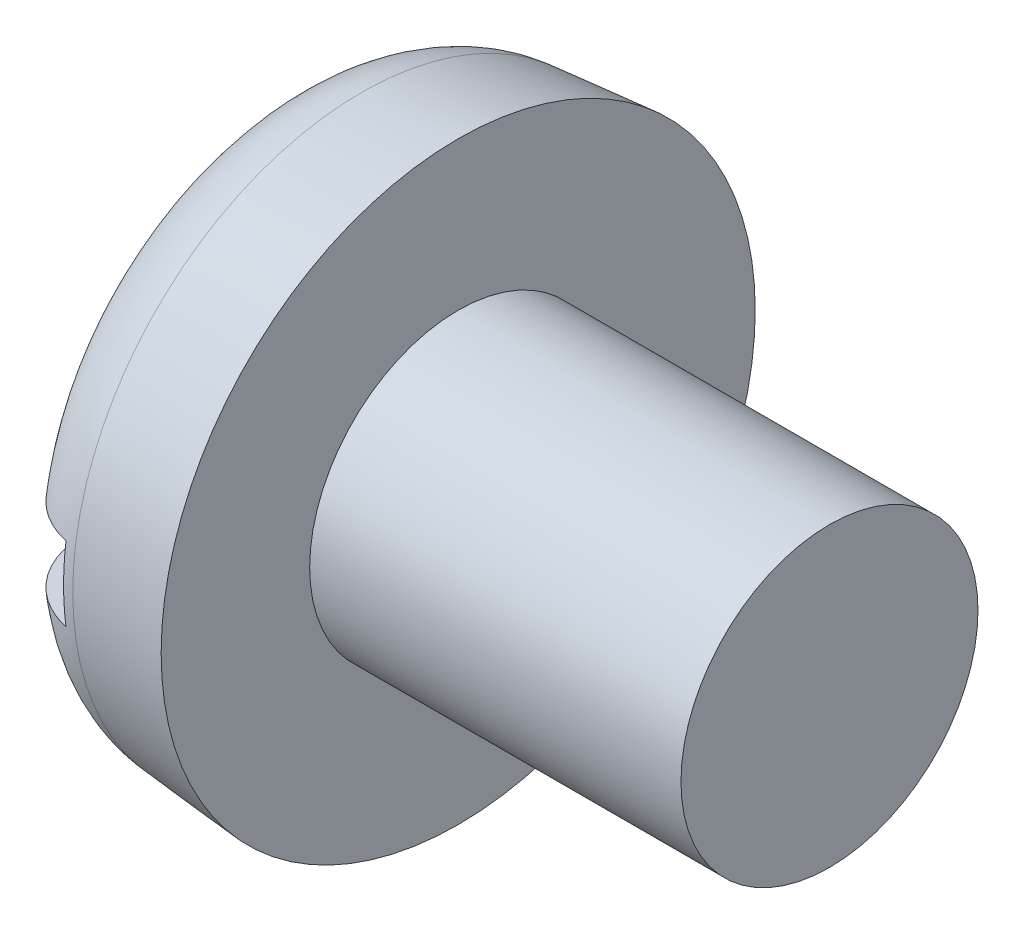
SolidWorks part; units mm, degrees
ref_plane "Plane1" through (0, 0, 0) normal (0, 0, 1) x (1, 0, 0)
ref_plane "Plane2" through (0, 0, 0) normal (0, 1, 0) x (1, 0, 0)
ref_plane "Plane3" through (0, 0, 0) normal (1, 0, 0) x (0, 0, -1)
sketch "BodySke" plane through (0, 0, 0) normal (0, 0, 1) x (1, 0, 0)
  line L0 (4.8, 4) -> (4.8, 8)
  line L1 (0, 0) -> (0, 7.5801)
  line L2 (-25.4, 0) -> (127, 0) construction
  line L3 (14.8, 0) -> (0, 0)
  line L4 (4.8, 4) -> (14.8, 4)
  line L5 (14.8, 4) -> (14.8, 0)
  line L6 (0, 7.5801) -> (4.8, 8)
  line L9 (6.05, 5.5875) -> (6.05, -3.9375) construction
  line L10 (4.8, 6.35) -> (4.8, -3.175) construction
  dimension "Head_ht" = 4.8
  dimension "Diameter" = 8
  dimension "Length" = 10
  dimension "Head_dia" = 16
  dimension "Advance" = 1.25
  dimension "Thread_nom" = 10
  dimension "Head_side_angle" = 5
revolve "Base-Revolve" add sketch "BodySke"
cosmetic thread "ThreadCosmetic"
fillet "Fillet1" [suppressed] radius 0.4
fillet "Fillet2" radius 2.4 1 edges at (0, 0, 7.5801)
sketch "Sketch2" plane through (0, 0, 0) normal (1, 0, 0) x (0, 0, -1)
  line L0 (8, -1) -> (-8, -1)
  line L1 (8, -1) -> (8, 1)
  line L2 (-8, 1) -> (8, 1)
  line L3 (-8, 1) -> (-8, -1)
  dimension "D1" = 16
  dimension "D2" = 8
  dimension "Slot_width" = 2
  dimension "D3" = 1
extrude "Slot" cut sketch "Sketch2" along normal blind 1.9
sketch "ThdSchSke" plane through (0, 0, 0) normal (0, 0, 1) x (1, 0, 0)
  line L0 (7.3, -3.3095) -> (6.8165, -4)
  line L1 (7.3, -3.3095) -> (7.7835, -4)
  line L2 (7.7835, -4) -> (7.7835, -5)
  line L3 (-3.175, 0) -> (5.1513, 0) construction
  line L5 (7.7835, -5) -> (6.8165, -5)
  line L6 (6.8165, -5) -> (6.8165, -4)
  dimension "Thread_minor" = 6.619
  dimension "Diameter" = 8
  dimension "Start" = 7.3
  dimension "SideAngle" = 55
  dimension "VeeAngle" = 70
  dimension "Overcut" = 10
revolve "ThreadSchematic" [suppressed] cut sketch "ThdSchSke" angle 360 about L3
pattern_linear "ThdSchPat" [suppressed]
equation "\"D1@Sketch2\" = \"Head_dia@BodySke\""
equation "\"D2@Sketch2\" = \"D1@Sketch2\" / 2"
equation "\"D3@Sketch2\" = \"Slot_width@Sketch2\" / 2"
equation "\"Thread_length@ThreadCosmetic\" = ((sgn( (\"Length@BodySke\" - \"Advance@BodySke\" * 2.0 ) - \"Thread_nom@BodySke\" )-1)*( (\"Length@BodySke\" - \"Advance@BodySke\"  * 2.0) - \"Thread_nom@BodySke\" ))/-2+ \"Thread_nom@BodySke\""
equation "\"Thread_minor@ThdSchSke\" = \"Thread_minor@ThreadCosmetic\""
equation "\"Diameter@ThdSchSke\" = \"Diameter@BodySke\""
equation "\"Overcut@ThdSchSke\" = \"Diameter@BodySke\" * 1.25"
equation "\"Start@ThdSchSke\" = \"Head_ht@BodySke\" + \"Length@BodySke\" - \"Thread_length@ThreadCosmetic\"  '---Non-countersunk---"
equation "\"Num_threads@ThdSchPat\" = int( \"Thread_length@ThreadCosmetic\" / \"Advance@BodySke\" + 0.999 )  + 1"
equation "\"Advance@ThdSchPat\" = \"Thread_length@ThreadCosmetic\" /  (\"Num_threads@ThdSchPat\" - 1) 'relax it"
